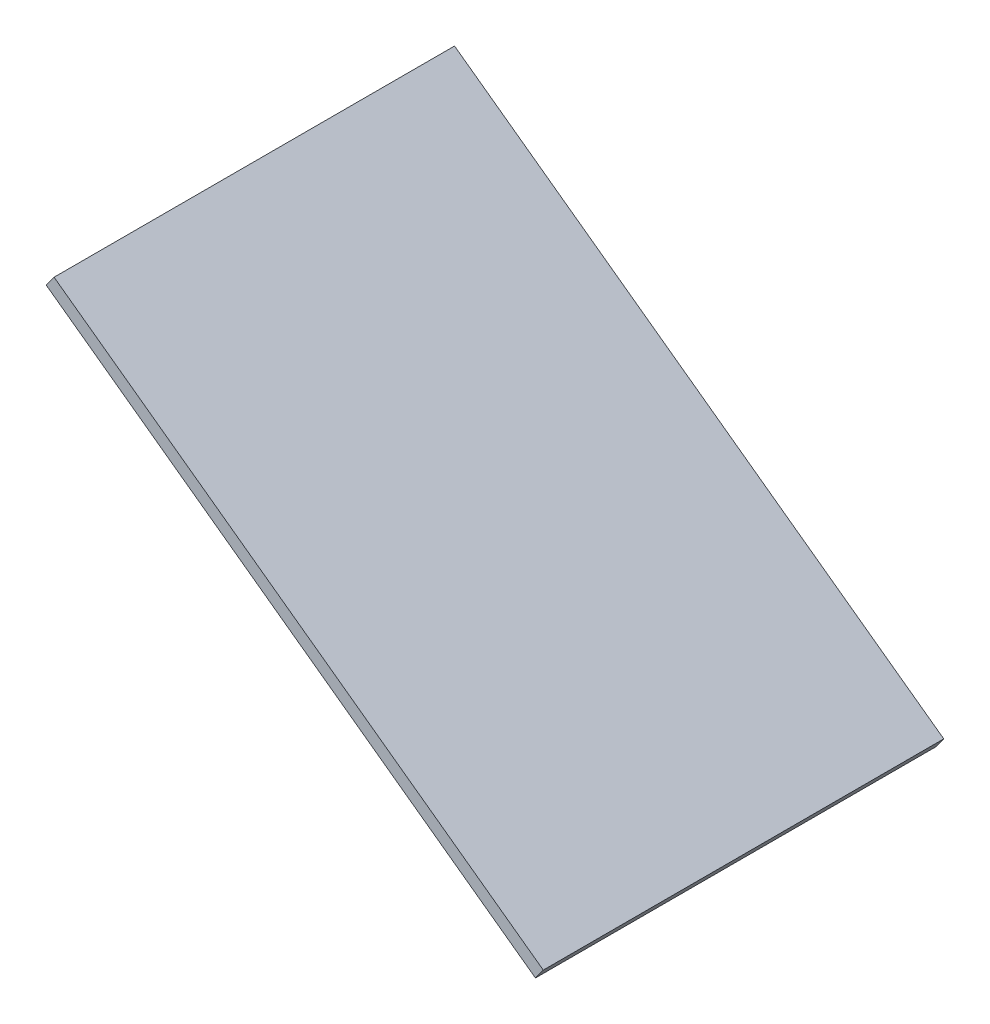
SolidWorks part; units mm, degrees
material "Alumina"
ref_plane "Front Plane" through (0, 0, 0) normal (0, 0, 1) x (1, 0, 0)
ref_plane "Top Plane" through (0, 0, 0) normal (0, 1, 0) x (1, 0, 0)
ref_plane "Right Plane" through (0, 0, 0) normal (1, 0, 0) x (0, 0, -1)
sketch "Sketch2" plane through (0, 0, 0) normal (0, 1, 0) x (1, 0, 0)
  line L0 (0, 45.186) -> (0, -54.814) construction
ref_plane "Plane1" through (0, 0, 0) normal (-0.5878, -0.809, 0) x (0, 0, 1)
sketch "Sketch3" plane through (0, 0, 0) normal (-0.5878, -0.809, 0) x (0, 0, 1)
  line L1 (-526.5, 1590) -> (526.5, 1590)
  line L2 (-526.5, 1590) -> (-526.5, 0)
  line L3 (-526.5, 0) -> (526.5, 0)
  line L4 (526.5, 1590) -> (526.5, 0)
  point P4 (0, 0)
extrude "Boss-Extrude1" add sketch "Sketch3" against normal blind 35
sketch "Sketch5" plane through (0, 0, 0) normal (-0.5878, -0.809, 0) x (0.809, -0.5878, 0)
  line L4 (-35, -491.5) -> (-1555, -491.5)
  line L5 (-35, -491.5) -> (-35, 491.5)
  line L6 (-35, 491.5) -> (-1555, 491.5)
  line L7 (-1555, -491.5) -> (-1555, 491.5)
  line L8 (-35, -491.5) -> (-1555, 491.5) construction
  line L9 (-35, 491.5) -> (-1555, -491.5) construction
  point P5 (-795, 0)
extrude "Cut-Extrude2" cut sketch "Sketch5" against normal blind 32
